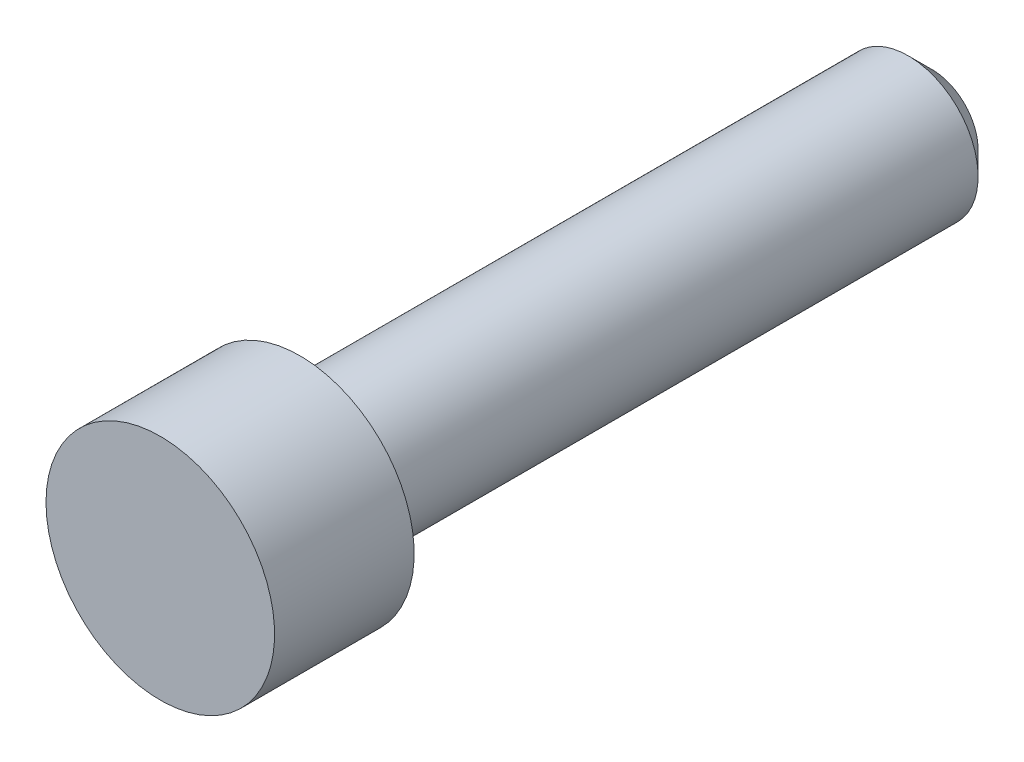
SolidWorks part; units mm, degrees
ref_plane "Front Plane" through (0, 0, 0) normal (0, 0, 1) x (1, 0, 0)
ref_plane "Top Plane" through (0, 0, 0) normal (0, 1, 0) x (1, 0, 0)
ref_plane "Right Plane" through (0, 0, 0) normal (1, 0, 0) x (0, 0, -1)
sketch "Sketch1" plane through (0, 0, 0) normal (1, 0, 0) x (0, 0, -1)
  line L0 (9.6901, 0) -> (-9.6901, 0) construction
  line L1 (-9.6901, 0) -> (-9.6901, 2.8702) construction
  line L2 (-6.1849, 1.7526) -> (-6.1849, 0) construction
  line L3 (8.8963, 0) -> (8.8963, 0.7938) construction
  line L4 (-6.1849, 0) -> (-6.1849, -1.7526) construction
  line L5 (9.6901, 1.7526) -> (9.6901, -1.7526) construction
  line L6 (-6.1849, 1.7526) -> (-6.1849, 2.8702) construction
  point P6 (-9.6901, 1.3891)
  point P9 (-9.6901, -1.3891)
  point P10 (-6.1849, 0)
  point P13 (6.912, -1.7526)
  dimension "Head Diameter" = 5.7404
  dimension "Head Height" = 3.5052
  dimension "Screw Size Decimal Equivalent" = 3.5052
  dimension "Length" = 15.875
  dimension "Pitch" = 0.7937
  dimension "Drive Size" = 2.7781
  dimension "D1" = 0.7937
  dimension "D2" = 2.7781
sketch "Sketch2" plane through (0, 0, 0) normal (1, 0, 0) x (0, 0, -1)
  line L0 (9.6901, 1.1573) -> (9.0948, 1.7526)
  line L1 (-9.6901, 2.8702) -> (-6.1849, 2.8702)
  line L2 (-9.6901, 2.8702) -> (-9.6901, 0)
  line L4 (-6.1849, 2.8702) -> (-6.1849, 1.7526)
  line L5 (-6.1849, 1.7526) -> (9.0948, 1.7526)
  line L8 (9.6901, 1.1573) -> (9.6901, 0)
  line L9 (9.6901, 0) -> (-9.6901, 0) construction
  line L10 (9.6901, 0) -> (-9.6901, 0)
  dimension "D1" = 135
  dimension "D2" = 0.5953
revolve "Revolve1" add sketch "Sketch2" angle 360 about L10
equation "\"Pitch Natural Taper Angle\"= ATN ( \"Pitch@Sketch1\" / 2 )"
equation "\"Rounded Angle Count\"= ROUND ( 60 / \"Pitch Natural Taper Angle\" )"
equation "\"Taper Angle\"= \"Rounded Angle Count\" * \"Pitch Natural Taper Angle\""
equation "\"D1@Sketch1\"=\"Pitch@Sketch1\""
equation "\"D2@Sketch2\"=\"D1@Sketch1\"*.75"
equation "\"D2@Sketch1\"=\"Pitch@Sketch1\"*3.5"
